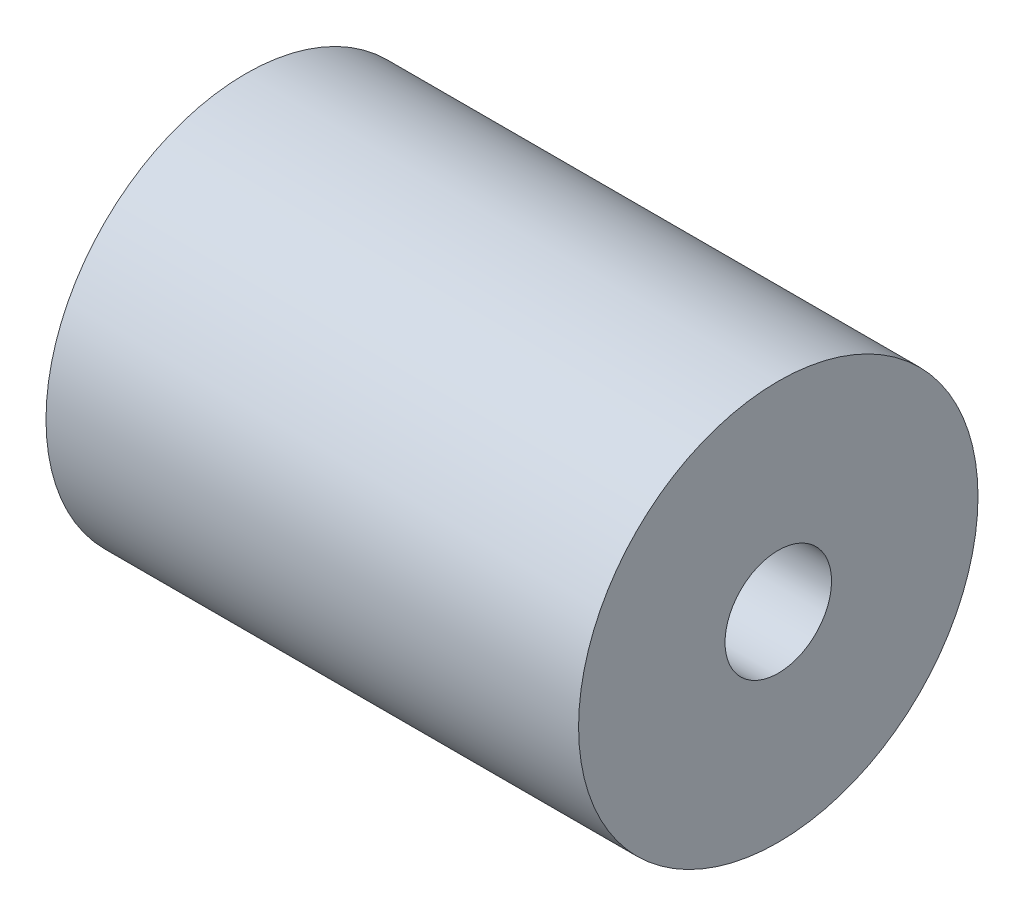
SolidWorks part; units mm, degrees
ref_plane "Front Plane" through (0, 0, 0) normal (0, 0, 1) x (1, 0, 0)
ref_plane "Top Plane" through (0, 0, 0) normal (0, 1, 0) x (1, 0, 0)
ref_plane "Right Plane" through (0, 0, 0) normal (1, 0, 0) x (0, 0, -1)
sketch "Sketch2" plane through (0, 0, 0) normal (1, 0, 0) x (0, 0, -1)
  circle A0 centre (0, 0) radius 7.5
  circle A1 centre (0, 0) radius 2
  dimension "D1" = 15
  dimension "D2" = 4
extrude "Boss-Extrude1" add sketch "Sketch2" along normal blind 20
